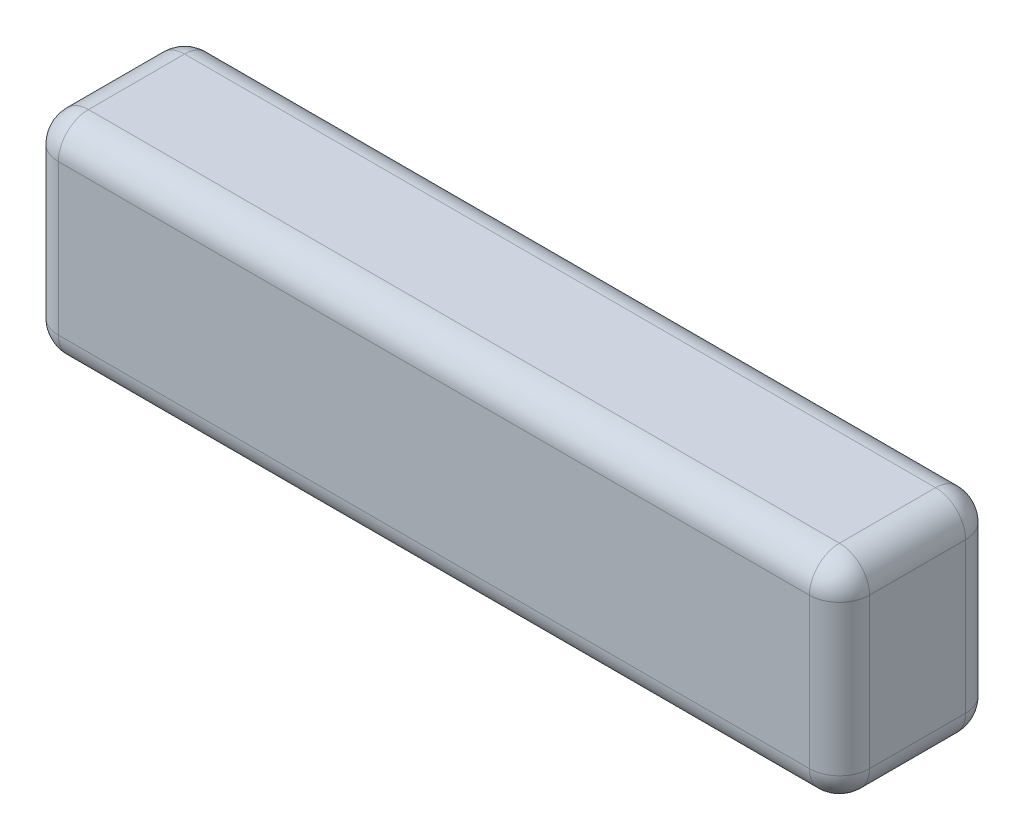
SolidWorks part; units mm, degrees
material "NEOPRENE"
ref_plane "Front Plane" through (0, 0, 0) normal (0, 0, 1) x (1, 0, 0)
ref_plane "Top Plane" through (0, 0, 0) normal (0, 1, 0) x (1, 0, 0)
ref_plane "Right Plane" through (0, 0, 0) normal (1, 0, 0) x (0, 0, -1)
sketch "Sketch1" plane through (0, 0, 0) normal (0, 0, 1) x (1, 0, 0)
  line L0 (0, 79.9039) -> (0, -69.9779) construction
  line L1 (-122.0891, 0) -> (112.1632, 0) construction
  line L2 (0, 0) -> (0, 35)
  line L3 (0, 35) -> (135, 35)
  line L4 (135, 35) -> (135, 0)
  line L5 (135, 0) -> (0, 0)
  dimension "D1" = 135
  dimension "D2" = 35
extrude "Boss-Extrude1" add sketch "Sketch1" along normal blind 26
fillet "Fillet1" radius 5 12 edges at (135, 17.5, 0) (67.5, 35, 0) (0, 17.5, 0) (67.5, 0, 0) (0, 0, 13) (0, 17.5, 26) (0, 35, 13) (135, 0, 13) (67.5, 0, 26) (135, 17.5, 26) (67.5, 35, 26) (135, 35, 13)
